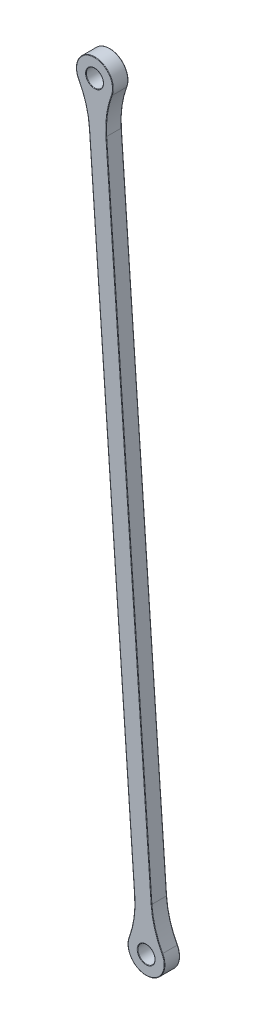
SolidWorks part; units mm, degrees
ref_plane "Front Plane" through (0, 0, 0) normal (0, 0, 1) x (1, 0, 0)
ref_plane "Top Plane" through (0, 0, 0) normal (0, 1, 0) x (1, 0, 0)
ref_plane "Right Plane" through (0, 0, 0) normal (1, 0, 0) x (0, 0, -1)
sketch "Sketch1" plane through (0, 0, 0) normal (0, 0, 1) x (1, 0, 0)
  line L0 (16.1627, 287.9649) -> (33.021, 48.5577) construction
  line L1 (16.1627, 287.9649) -> (33.021, 48.5577) construction
  line L2 (33.021, 48.5577) -> (16.1627, 287.9649) construction
  line L3 (30.2279, 48.3611) -> (13.3696, 287.7682)
  line L4 (35.814, 48.7544) -> (18.9558, 288.1616)
  circle A0 centre (16.1627, 287.9649) radius 6
  circle A1 centre (33.021, 48.5577) radius 6
  arc A2 (30.2279, 48.3611) -> (35.814, 48.7544) centre (33.021, 48.5577) ccw
  arc A3 (18.9558, 288.1616) -> (13.3696, 287.7682) centre (16.1627, 287.9649) ccw
  arc A4 (13.3696, 287.7682) -> (18.9558, 288.1616) centre (16.1627, 287.9649) ccw
  arc A5 (35.814, 48.7544) -> (30.2279, 48.3611) centre (33.021, 48.5577) ccw
  point P5 (24.5918, 168.2613)
  dimension "D1" = 12
  dimension "D2" = 5.6
extrude "Boss-Extrude1" add sketch "Sketch1" against normal blind 5 contours A3 L4 A0 L3 | A4 L3 A0 L4 | A2 L3 A1 L4 | A5 L4 A1 L3 | A1 L4 A0 L3
fillet "Fillet1" radius 30 4 edges at (19.3285, 282.8681, -2.5) (13.7423, 282.4748, -2.5) (29.8551, 53.6546, -2.5) (35.4413, 54.0479, -2.5)
fillet "Fillet2" radius 0.15 20 edges at (35.821, 48.5577, -5) (35.821, 48.5577, 0) (18.9627, 287.9649, -5) (18.9627, 287.9649, 0) (35.8886, 57.294, -5) (35.8886, 57.294, 0) (27.3849, 168.458, -5) (27.3849, 168.458, 0) (20.2263, 279.7168, -5) (20.2263, 279.7168, 0) (15.7412, 293.9501, 0) (15.7412, 293.9501, -5) (13.295, 279.2287, -5) (13.295, 279.2287, 0) (21.7987, 168.0647, 0) (21.7987, 168.0647, -5) (28.9573, 56.8059, -5) (28.9573, 56.8059, 0) (33.4424, 42.5726, 0) (33.4424, 42.5726, -5)
